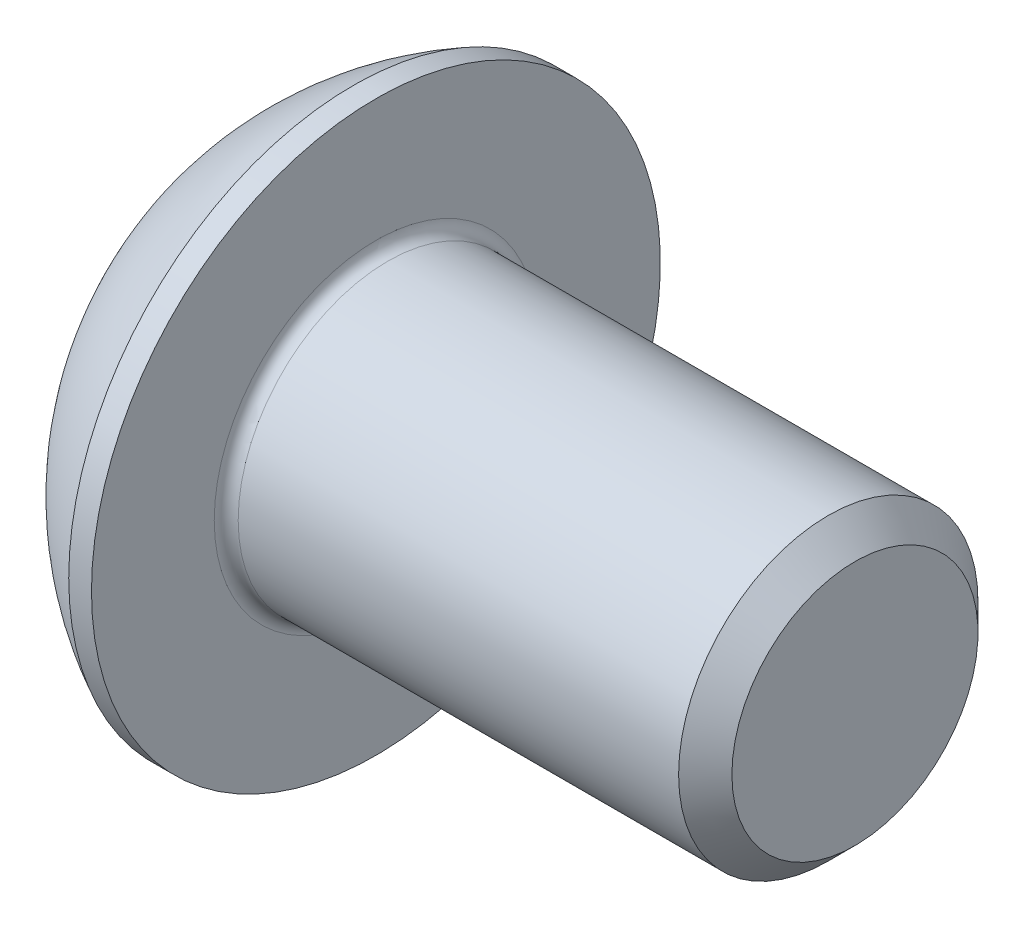
SolidWorks part; units mm, degrees
ref_plane "Plane1" through (0, 0, 0) normal (0, 0, 1) x (1, 0, 0)
ref_plane "Plane2" through (0, 0, 0) normal (0, 1, 0) x (1, 0, 0)
ref_plane "Plane3" through (0, 0, 0) normal (1, 0, 0) x (0, 0, -1)
sketch "BodySke" plane through (0, 0, 0) normal (0, 0, 1) x (1, 0, 0)
  line L0 (10.75, 0) -> (10.75, 2.055)
  line L1 (10.305, 2.5) -> (2.75, 2.5)
  line L2 (2.75, 2.5) -> (2.75, 4.75)
  line L3 (2.75, 4.75) -> (2.37, 4.75)
  line L4 (0, 0) -> (101.6, 0) construction
  line L5 (2.75, -4.75) -> (2.37, -4.75) construction
  line L6 (55.6768, -2.5) -> (2.75, -2.5) construction
  line L7 (10.75, 0) -> (0, 0)
  line L8 (0, 2.375) -> (0, -2.375) construction
  line L9 (0, 0) -> (0, 2.375)
  line L10 (10.75, 2.055) -> (10.305, 2.5)
  line L11 (10.75, -2.055) -> (10.305, -2.5) construction
  line L12 (3.55, 9.525) -> (3.55, -2.5) construction
  line L13 (2.75, 9.525) -> (2.75, -2.5) construction
  arc A1 (0, 2.375) -> (2.37, 4.75) centre (4.755, 0) cw
  dimension "Diameter" = 5
  dimension "Length" = 8
  dimension "Head_dia" = 9.5
  dimension "D1" = 4.75
  dimension "Head_ht" = 2.75
  dimension "Head_side_ht" = 0.38
  dimension "Minor_dia" = 4.11
  dimension "Body_ch_ang" = 45
  dimension "Advance" = 0.8
  dimension "Thread_nom" = 8
revolve "BaseBody" add sketch "BodySke" angle 360 about L4
cosmetic thread "ThreadCosmetic" [suppressed] parameters "Thread_length"=6.4, "Thread_minor"=4.11
fillet "Fillet1" radius 0.2 1 edges at (2.75, 0, 2.5)
sketch "Sketch2" plane through (0, 0, 0) normal (0, 0, 1) x (1, 0, 0)
  line L0 (0, 1.5) -> (1.56, 1.5)
  line L1 (1.56, 1.5) -> (2.426, 0)
  line L3 (2.426, 0) -> (0, 0)
  line L4 (0, 0) -> (0, 1.5)
  line L5 (0, -1.5) -> (1.56, -1.5) construction
  line L6 (0, 0) -> (47.625, 0) construction
  dimension "D2" = 60
  dimension "PreBroach_depth" = 1.56
  dimension "PreBroach_dia" = 3
revolve "PreBroach" cut sketch "Sketch2" angle 360 about L6
sketch "Sketch3" plane through (0, 0, 0) normal (1, 0, 0) x (0, 0, -1)
  line L0 (-1.5, -0.866) -> (-1.5, 0.866)
  line L1 (-1.5, 0.866) -> (0, 1.7321)
  line L2 (0, 1.7321) -> (1.5, 0.866)
  line L3 (1.5, 0.866) -> (1.5, -0.866)
  line L4 (1.5, -0.866) -> (0, -1.7321)
  line L5 (0, -1.7321) -> (-1.5, -0.866)
  dimension "Hex_size" = 3
  dimension "D3" = 3
  dimension "D1" = 1.5
  dimension "D2" = 1.5
extrude "Hex" cut sketch "Sketch3" along normal blind 1.56
sketch "ThdSchSke" plane through (0, 0, 0) normal (0, 0, 1) x (1, 0, 0)
  line L0 (4.35, -2.055) -> (4.0384, -2.5)
  line L1 (4.35, -2.055) -> (4.6616, -2.5)
  line L2 (4.6616, -2.5) -> (4.6616, -3.125)
  line L3 (-3.175, 0) -> (5.1513, 0) construction
  line L5 (4.6616, -3.125) -> (4.0384, -3.125)
  line L6 (4.0384, -3.125) -> (4.0384, -2.5)
  dimension "Diameter" = 5
  dimension "Thread_minor" = 4.11
  dimension "SideAngle" = 55
  dimension "VeeAngle" = 70
  dimension "Overcut" = 6.25
  dimension "Start" = 4.35
revolve "ThreadSchematic" [suppressed] cut sketch "ThdSchSke" angle 360 about L3
pattern_linear "ThdSchPat" [suppressed]
equation "\"D1@BodySke\" = \"Head_dia@BodySke\" * .5"
equation "\"Thread_minor@ThreadCosmetic\" = \"Minor_dia@BodySke\""
equation "\"D1@Sketch3\" = \"Hex_size@Sketch3\" / 2"
equation "\"D2@Sketch3\" = \"D1@Sketch3\""
equation "\"D3@Sketch3\" = \"Hex_size@Sketch3\""
equation "\"Thread_length@ThreadCosmetic\" = ((sgn( (\"Length@BodySke\" - \"Advance@BodySke\" * 2.0) - \"Thread_nom@BodySke\" )-1)*( (\"Length@BodySke\" - \"Advance@BodySke\" * 2.0) - \"Thread_nom@BodySke\" ))/-2+ \"Thread_nom@BodySke\""
equation "\"Thread_minor@ThdSchSke\" = \"Minor_dia@BodySke\""
equation "\"Diameter@ThdSchSke\" = \"Diameter@BodySke\""
equation "\"Overcut@ThdSchSke\" = \"Diameter@BodySke\" * 1.25"
equation "\"Start@ThdSchSke\" = \"Head_ht@BodySke\" + \"Length@BodySke\" - \"Thread_length@ThreadCosmetic\"  '---Non-countersunk---"
equation "\"Num_threads@ThdSchPat\" = int( \"Thread_length@ThreadCosmetic\" / \"Advance@BodySke\" + 0.999 )  + 1"
equation "\"Advance@ThdSchPat\" = \"Thread_length@ThreadCosmetic\" /  (\"Num_threads@ThdSchPat\" - 1) 'relax it"
equation "\"Num_threads@ThdSchPat\" = \"Num_threads@ThdSchPat\" - sgn( \"Num_threads@ThdSchPat\" - 1) '---chamfered tips only---"
